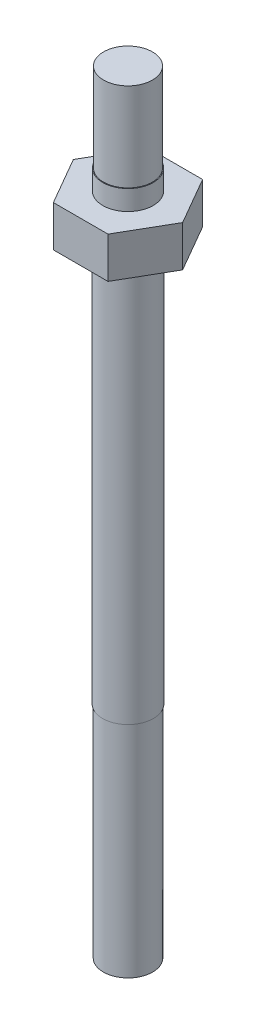
SolidWorks part; units mm, degrees
ref_plane "Front Plane" through (0, 0, 0) normal (0, 0, 1) x (1, 0, 0)
ref_plane "Top Plane" through (0, 0, 0) normal (0, 1, 0) x (1, 0, 0)
ref_plane "Right Plane" through (0, 0, 0) normal (1, 0, 0) x (0, 0, -1)
sketch "Sketch1" plane through (0, 0, 0) normal (0, 1, 0) x (1, 0, 0)
  circle A0 centre (0, 0) radius 1.7145
  dimension "D1" = 3.429
extrude "Boss-Extrude1" add sketch "Sketch1" against normal blind 42.0878
sketch "Sketch2" plane through (0, 0, 0) normal (0, 1, 0) x (1, 0, 0)
  line L0 (0, 3.1953) -> (0, 0) construction
  line L1 (1.8448, 3.1953) -> (-1.8448, 3.1953)
  line L2 (-1.8448, 3.1953) -> (-3.6896, 0)
  line L3 (-3.6896, 0) -> (-1.8448, -3.1953)
  line L4 (-1.8448, -3.1953) -> (1.8448, -3.1953)
  line L5 (1.8448, -3.1953) -> (3.6896, 0)
  line L6 (3.6896, 0) -> (1.8448, 3.1953)
  circle A0 centre (0, 0) radius 3.1953 construction
extrude "Boss-Extrude2" add sketch "Sketch2" along normal blind 2.7686
sketch "Sketch3" plane through (0, 2.7686, 0) normal (0, 1, 0) x (1, 0, 0)
  circle A0 centre (0, 0) radius 1.7018
  dimension "D1" = 3.4036
extrude "Boss-Extrude3" add sketch "Sketch3" along normal blind 7.3152
sketch "Sketch4" plane through (0, 10.0838, 0) normal (0, 1, 0) x (1, 0, 0)
  circle A1 centre (0, 0) radius 1.7018 construction
  circle A2 centre (0, 0) radius 1.651
  circle A3 centre (0, 0) radius 1.651
  circle A4 centre (0, 0) radius 1.7018
  dimension "D1" = 0.0508
extrude "Cut-Extrude1" cut sketch "Sketch4" against normal blind 5.969
sketch "Sketch5" plane through (0, -42.0878, 0) normal (0, -1, 0) x (1, 0, 0)
  circle A0 centre (0, 0) radius 1.6637
  circle A1 centre (0, 0) radius 1.7145
  circle A2 centre (0, 0) radius 1.7145
  dimension "D1" = 0
  dimension "D2" = 0.0508
extrude "Cut-Extrude2" cut sketch "Sketch5" against normal blind 14.859
